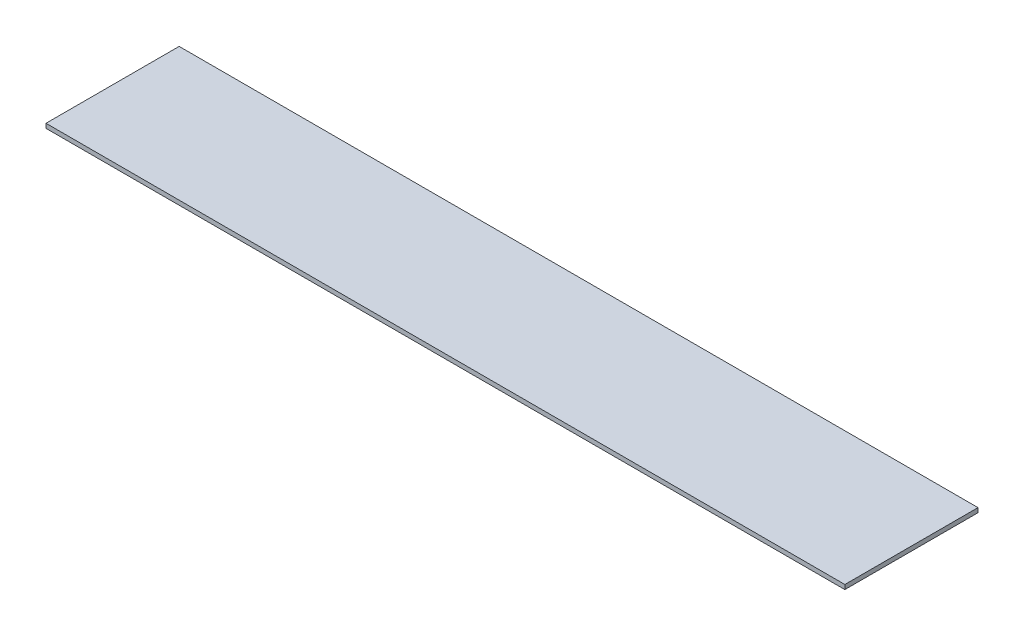
SolidWorks part; units mm, degrees
ref_plane "Front Plane" through (0, 0, 0) normal (0, 0, 1) x (1, 0, 0)
ref_plane "Top Plane" through (0, 0, 0) normal (0, 1, 0) x (1, 0, 0)
ref_plane "Right Plane" through (0, 0, 0) normal (1, 0, 0) x (0, 0, -1)
sketch "Sketch1" plane through (0, 0, 0) normal (0, 1, 0) x (1, 0, 0)
  line L1 (-450, -75) -> (450, -75)
  line L2 (-450, -75) -> (-450, 75)
  line L3 (-450, 75) -> (450, 75)
  line L4 (450, -75) -> (450, 75)
  line L5 (-450, -75) -> (450, 75) construction
  line L6 (-450, 75) -> (450, -75) construction
  point P0 (0, 0)
  dimension "D1" = 900
  dimension "D2" = 150
extrude "Boss-Extrude1" add sketch "Sketch1" along normal blind 5
